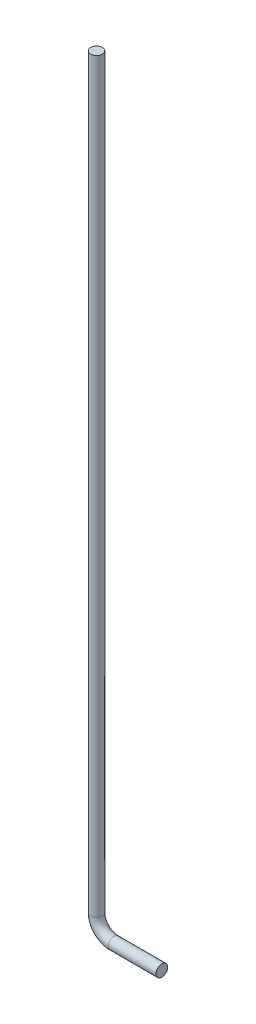
SolidWorks part; units mm, degrees
ref_plane "Front Plane" through (0, 0, 0) normal (0, 0, 1) x (1, 0, 0)
ref_plane "Top Plane" through (0, 0, 0) normal (0, 1, 0) x (1, 0, 0)
ref_plane "Right Plane" through (0, 0, 0) normal (1, 0, 0) x (0, 0, -1)
sketch "Sketch1" plane through (0, 0, 0) normal (0, 1, 0) x (1, 0, 0)
  line L0 (0, 0) -> (-12.7, 0) construction
  circle A0 centre (-12.7, 0) radius 1.5875
  dimension "D2" = 3.175
  dimension "D1" = 12.7
extrude "Boss-Extrude1" add sketch "Sketch1" against normal blind 203.2
sketch "Sketch2" plane through (0, 0, 0) normal (0, 0, 1) x (1, 0, 0)
  line L0 (-14.2875, -203.2) -> (-11.1125, -203.2) construction
  line L4 (-14.2875, -203.2) -> (-11.1125, -203.2) construction
  line L6 (-11.1125, -203.2) -> (-11.1125, -224.852) construction
  line L7 (-11.1125, -203.2) -> (-11.1125, 0) construction
  line L8 (-14.2875, -203.2) -> (-14.2875, -224.852) construction
  line L9 (-14.2875, 0) -> (-14.2875, -203.2) construction
  line L10 (-7.9375, -206.375) -> (0, -206.375) construction
  line L11 (0, -206.375) -> (5.08, -206.375) construction
  line L12 (5.08, -206.375) -> (5.08, -209.55) construction
  line L13 (5.08, -209.55) -> (0, -209.55) construction
  line L14 (0, -209.55) -> (-7.9375, -209.55) construction
  line L15 (0, -206.375) -> (0, 0) construction
  line L16 (-7.9375, -206.375) -> (-7.9375, -209.55) construction
  line L17 (-7.9375, -207.9625) -> (5.08, -207.9625)
  arc A0 (-11.1125, -203.2) -> (-7.9375, -206.375) centre (-7.9375, -203.2) ccw construction
  arc A1 (-14.2875, -203.2) -> (-7.9375, -209.55) centre (-7.9375, -203.2) ccw construction
  arc A2 (-7.9375, -207.9625) -> (-12.7, -203.2) centre (-7.9375, -203.2) cw
  point P20 (5.08, -233.3625)
  dimension "D1" = 3.175
  dimension "D2" = 3.175
  dimension "D3" = 5.08
ref_plane "Plane1" through (5.08, 0, 0) normal (1, 0, 0) x (0, 0, -1)
sketch "Sketch3" plane through (5.08, 0, 0) normal (1, 0, 0) x (0, 0, -1)
  line L0 (0, -206.375) -> (0, -209.55) construction
  line L1 (0, -206.375) -> (0, -209.55) construction
  circle A0 centre (0, -207.9625) radius 1.5875
sweep "Sweep1" add profiles "Sketch3" path "Sketch2"
